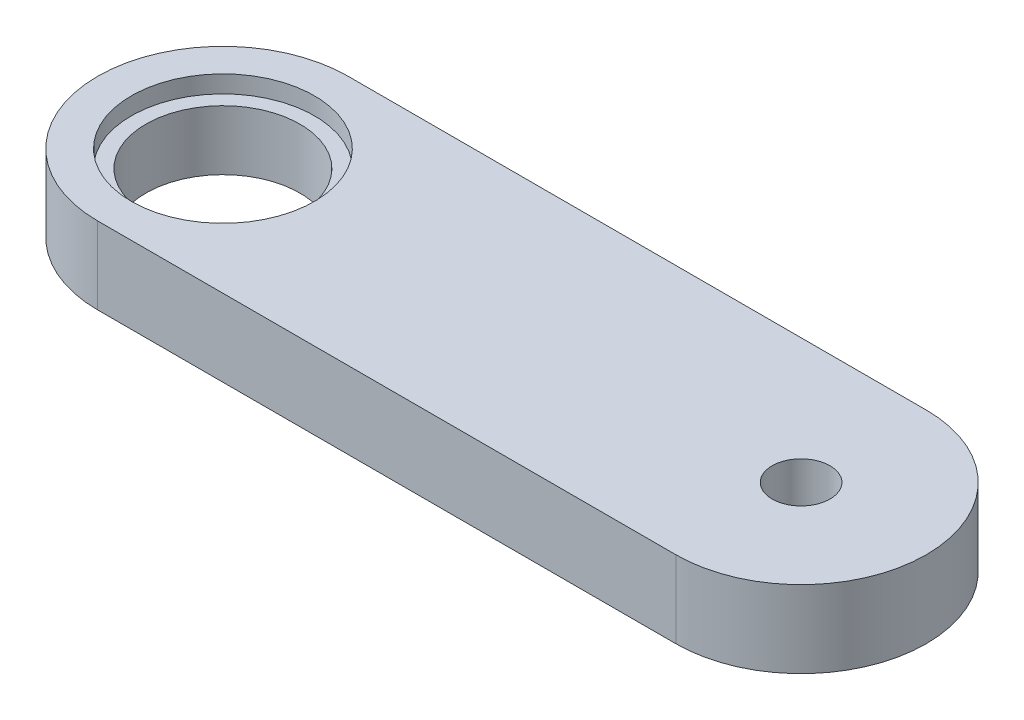
SolidWorks part; units mm, degrees
ref_plane "前视基准面" through (0, 0, 0) normal (0, 0, 1) x (1, 0, 0)
ref_plane "上视基准面" through (0, 0, 0) normal (0, 1, 0) x (1, 0, 0)
ref_plane "右视基准面" through (0, 0, 0) normal (1, 0, 0) x (0, 0, -1)
other "Configuration Table"
sketch "草图1" plane through (0, 0, 0) normal (0, 1, 0) x (1, 0, 0)
  line L0 (0, 0) -> (30, 0) construction
  line L1 (0, 6.5) -> (30, 6.5)
  line L2 (0, -6.5) -> (30, -6.5)
  arc A0 (0, 6.5) -> (0, -6.5) centre (0, 0) ccw
  arc A1 (30, -6.5) -> (30, 6.5) centre (30, 0) ccw
  point P3 (15, 0)
  dimension "D1" = 6.5
  dimension "D2" = 30
extrude "凸台-拉伸1" add sketch "草图1" along normal blind 4
sketch "草图2" plane through (0, 4, 0) normal (0, 1, 0) x (1, 0, 0)
  point P0 (0, 0)
hole_wizard "M5 六角头螺栓的柱形沉头孔1" positions "草图2" profile "草图3" counterbore size "M5" standard "GB"
sketch "草图3" plane through (0, 4, 0) normal (1, 0, 0) x (0, 0, 1)
  line L0 (0, 0) -> (0, 14.8034)
  line L1 (0, 14.8034) -> (4, 12.4)
  line L2 (4, 12.4) -> (4, 0.9)
  line L3 (4, 0.9) -> (4.75, 0.9)
  line L4 (4.75, 0.9) -> (4.75, 0)
  line L5 (4.75, 0) -> (0, 0)
  line L10 (0, 14.8034) -> (-4, 12.4) construction
  line L11 (0, -6.35) -> (0, 107.95) construction
  dimension "孔直径" = 8
  dimension "孔深度" = 12.4
  dimension "柱形沉头孔直径" = 9.5
  dimension "柱形沉头孔深度" = 0.9
  dimension "导头角度" = 118
sketch "草图4" plane through (0, 4, 0) normal (0, 1, 0) x (1, 0, 0)
  circle A0 centre (30, 0) radius 1.5
  dimension "D1" = 3
extrude "切除-拉伸1" cut sketch "草图4" against normal through all both and the other way through all
